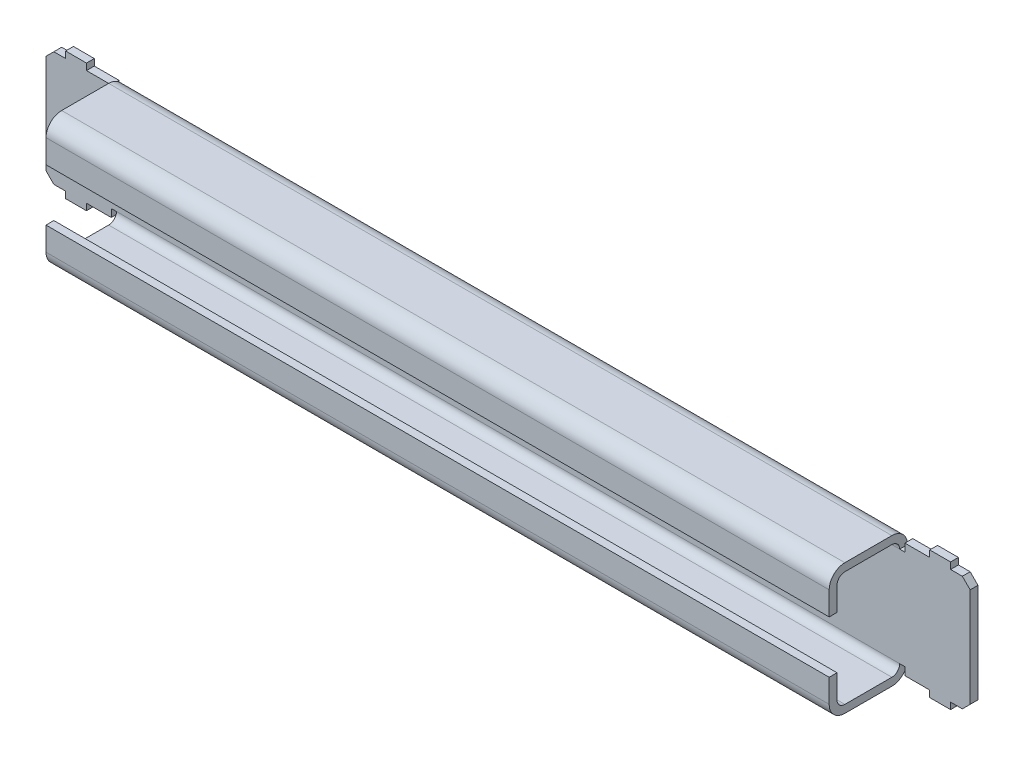
SolidWorks part; units mm, degrees
ref_plane "Front Plane" through (0, 0, 0) normal (0, 0, 1) x (1, 0, 0)
ref_plane "Top Plane" through (0, 0, 0) normal (0, 1, 0) x (1, 0, 0)
ref_plane "Right Plane" through (0, 0, 0) normal (1, 0, 0) x (0, 0, -1)
sketch "Sketch2" plane through (0, 0, 0) normal (1, 0, 0) x (0, 0, -1)
  line L0 (0, 0) -> (30, 0)
  line L1 (30, 0) -> (30, 50)
  line L2 (30, 50) -> (0, 50)
  line L3 (0, 50) -> (0, 35)
  line L4 (0, 0) -> (0, 15)
  line L5 (3, 3) -> (3, 15)
  line L6 (3, 3) -> (27, 3)
  line L7 (27, 3) -> (27, 47)
  line L8 (27, 47) -> (3, 47)
  line L9 (3, 47) -> (3, 35)
  line L10 (0, 35) -> (3, 35)
  line L11 (0, 15) -> (3, 15)
  dimension "D1" = 30
  dimension "D2" = 50
  dimension "D4" = 15
  dimension "D5" = 3
extrude "Boss-Extrude1" add sketch "Sketch2" along normal mid plane 300
fillet "Fillet1" radius 6 4 edges at (0, 50, -30) (0, 0, -30) (0, 0, 0) (0, 50, 0)
fillet "Fillet2" radius 3 4 edges at (0, 3, -3) (0, 3, -27) (0, 47, -27) (0, 47, -3)
sketch "Sketch3" plane through (0, 0, -27) normal (0, 0, 1) x (1, 0, 0)
  line L0 (-150, 44) -> (-152, 44)
  line L1 (-150, 44) -> (-150, 35) construction
  line L2 (-152, 44) -> (-152, 47)
  line L10 (-152, 3) -> (-152, 6)
  line L11 (-152, 6) -> (-150, 6)
  line L12 (-150, 15) -> (-150, 6) construction
  line L13 (-150, 6) -> (-150, 44)
  line L14 (150, 50) -> (-150, 50) construction
  line L15 (-152, 47) -> (-161.5, 47)
  line L18 (-150, 50) -> (-150, 44) construction
  line L19 (0, 0) -> (0, 90.7887) construction
  line L20 (150, 0) -> (-150, 0) construction
  line L35 (-161.5, 47) -> (-161.5, 49.5)
  line L36 (-161.5, 49.5) -> (-169.5, 49.5)
  line L37 (-169.5, 49.5) -> (-169.5, 47)
  line L38 (-169.5, 47) -> (-174, 47)
  line L39 (-161.5, 3) -> (-152, 3)
  line L40 (-161.5, 3) -> (-161.5, 0.5)
  line L41 (-161.5, 0.5) -> (-169.5, 0.5)
  line L42 (-169.5, 0.5) -> (-169.5, 3)
  line L43 (-169.5, 3) -> (-174, 3)
  line L44 (-177, 6) -> (-177, 44)
  line L61 (-174, 47) -> (-177, 44)
  line L62 (-174, 3) -> (-177, 6)
  line L63 (174, 3) -> (177, 6)
  line L64 (174, 47) -> (177, 44)
  line L65 (177, 6) -> (177, 44)
  line L66 (169.5, 3) -> (174, 3)
  line L67 (169.5, 0.5) -> (169.5, 3)
  line L68 (161.5, 0.5) -> (169.5, 0.5)
  line L69 (161.5, 3) -> (161.5, 0.5)
  line L70 (161.5, 3) -> (152, 3)
  line L71 (169.5, 47) -> (174, 47)
  line L72 (169.5, 49.5) -> (169.5, 47)
  line L73 (161.5, 49.5) -> (169.5, 49.5)
  line L74 (161.5, 47) -> (161.5, 49.5)
  line L75 (152, 47) -> (161.5, 47)
  line L76 (150, 6) -> (150, 44)
  line L77 (152, 6) -> (150, 6)
  line L78 (152, 3) -> (152, 6)
  line L79 (152, 44) -> (152, 47)
  line L80 (150, 44) -> (152, 44)
  point P11 (-177, 47)
  point P24 (-177, 3)
  point P46 (0, 0)
  point P52 (177, 3)
  point P53 (177, 47)
  dimension "D1" = 3
  dimension "D2" = 6
  dimension "D3" = 9.5
  dimension "D4" = 2
  dimension "D5" = 6
  dimension "D6" = 2.5
  dimension "D7" = 8
  dimension "D8" = 27
extrude "Boss-Extrude2" add sketch "Sketch3" against normal up to surface (3 mm away) up to face at (0, 25, -30)
